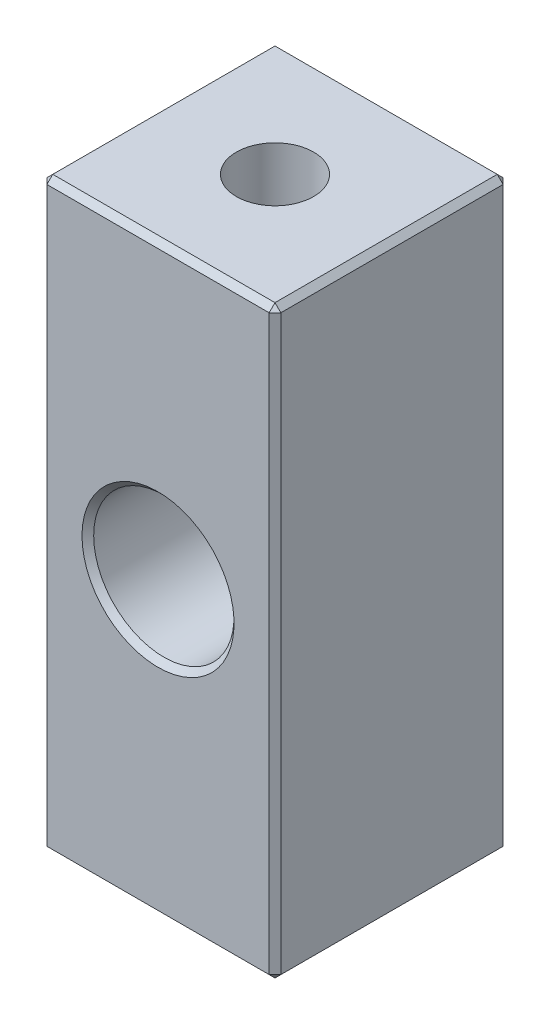
SolidWorks part; units mm, degrees
material "1060 Alloy"
ref_plane "Front Plane" through (0, 0, 0) normal (0, 0, 1) x (1, 0, 0)
ref_plane "Top Plane" through (0, 0, 0) normal (0, 1, 0) x (1, 0, 0)
ref_plane "Right Plane" through (0, 0, 0) normal (1, 0, 0) x (0, 0, -1)
sketch "Sketch1" plane through (0, 0, 0) normal (0, 0, 1) x (1, 0, 0)
  line L0 (-5, -12.5) -> (5, 12.5) construction
  line L1 (-5, -12.5) -> (5, -12.5)
  line L2 (-5, -12.5) -> (-5, 12.5)
  line L3 (-5, 12.5) -> (5, 12.5)
  line L4 (5, -12.5) -> (5, 12.5)
  point P4 (0, 0)
  dimension "D1" = 25
  dimension "D2" = 10
extrude "Extrude1" add sketch "Sketch1" along normal blind 10
sketch "Sketch2" plane through (0, 0, 10) normal (0, 0, 1) x (1, 0, 0)
  circle A0 centre (0, 0) radius 3
  dimension "D1" = 6
extrude "Cut-Extrude1" cut sketch "Sketch2" against normal blind 10
hole_wizard "M4x0.7 Tapped Hole1" positions "3DSketch1" profile "Sketch3" tap size "M4x0.7" standard "Ansi Metric"
sketch3d "3DSketch1"
  line L0 (-5, 12.5, 10) -> (-5, 12.5, 0) construction
  line L1 (5, 12.5, 0) -> (-5, 12.5, 0) construction
  point P0 (0, 12.5, 5)
  point P2 (0, -12.5, 5)
  dimension "D1" = 5
  dimension "D2" = 5
sketch "Sketch3" plane through (0, 12.5, 5) normal (1, 0, 0) x (0, 0, 1)
  line L0 (0, 0) -> (0, 8.9914)
  line L1 (0, 8.9914) -> (1.65, 8)
  line L2 (1.65, 8) -> (1.65, 0)
  line L5 (1.65, 0) -> (0, 0)
  line L10 (0, 8.9914) -> (-1.65, 8) construction
  line L11 (0, -6.35) -> (0, 107.95) construction
  dimension "Tap Drill Dia." = 3.3
  dimension "Tap Drill Depth" = 8
  dimension "Drill Angle" = 118
cosmetic thread "Hole Thread1" parameters "D1"=8, "D2"=4
cosmetic thread "Hole Thread2" parameters "D1"=8, "D2"=4
chamfer "Chamfer1" distance 0.25 angle 45 14 edges at (3, 0, 0) (-5, 12.5, 5) (-5, -12.5, 5) (0, -12.5, 0) (-5, 0, 0) (0, 12.5, 0) (5, -12.5, 5) (5, 0, 0) (5, 12.5, 5) (0, 12.5, 10) (5, 0, 10) (0, -12.5, 10) (-5, 0, 10) (3, 0, 10)
